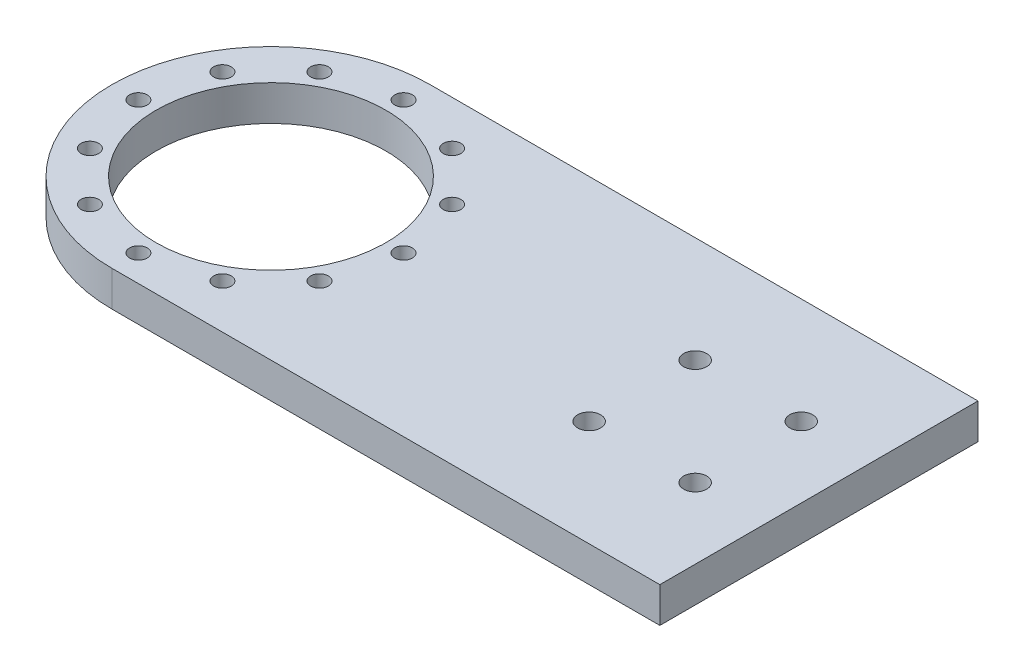
SolidWorks part; units mm, degrees
ref_plane "Front Plane" through (0, 0, 0) normal (0, 0, 1) x (1, 0, 0)
ref_plane "Top Plane" through (0, 0, 0) normal (0, 1, 0) x (1, 0, 0)
ref_plane "Right Plane" through (0, 0, 0) normal (1, 0, 0) x (0, 0, -1)
sketch "Sketch1" plane through (0, 0, 0) normal (0, 1, 0) x (1, 0, 0)
  line L0 (-55, 45) -> (100, 45)
  line L1 (-100, -45) -> (100, -45) construction
  line L2 (-100, -45) -> (-100, 45) construction
  line L3 (-100, 45) -> (100, 45) construction
  line L4 (100, -45) -> (100, 45) construction
  line L5 (0, 45) -> (0, -45) construction
  line L6 (-100, 0) -> (100, 0) construction
  line L7 (100, 45) -> (100, -45)
  line L8 (100, -45) -> (-55, -45)
  arc A1 (-55, 45) -> (-54.7588, -44.9994) centre (-55, 0) ccw
  point P0 (0, 0)
  dimension "D1" = 90
  dimension "D2" = 200
extrude "Boss-Extrude1" add sketch "Sketch1" along normal blind 10
sketch "Sketch2" plane through (0, 10, 0) normal (0, 1, 0) x (1, 0, 0)
  circle A0 centre (-55, 0) radius 37.5 construction
  circle A1 centre (-92.5, 0) radius 2.5
  circle A2 centre (-87.476, 18.75) radius 2.5
  circle A3 centre (-73.75, 32.476) radius 2.5
  circle A4 centre (-55, 0) radius 32.5
  circle A5 centre (-55, 37.5) radius 2.5
  circle A6 centre (-36.25, 32.476) radius 2.5
  circle A7 centre (-22.524, 18.75) radius 2.5
  circle A8 centre (-17.5, 0) radius 2.5
  circle A9 centre (-22.524, -18.75) radius 2.5
  circle A10 centre (-36.25, -32.476) radius 2.5
  circle A11 centre (-55, -37.5) radius 2.5
  circle A12 centre (-73.75, -32.476) radius 2.5
  circle A13 centre (-87.476, -18.75) radius 2.5
  point P11 (-55, 0)
  dimension "D1" = 75
  dimension "D2" = 5
  dimension "D4" = 65
  dimension "D3" = 12
extrude "Cut-Extrude1" cut sketch "Sketch2" against normal through all
sketch "Sketch3" plane through (0, 10, 0) normal (0, 1, 0) x (1, 0, 0)
  line L0 (100, 0) -> (-100, 0) construction
  line L1 (100, 45) -> (100, -45) construction
  line L3 (50, -15) -> (80, -15)
  line L4 (50, -15) -> (50, 15)
  line L5 (50, 15) -> (80, 15)
  line L6 (80, -15) -> (80, 15)
  line L7 (65, 15) -> (65, -15) construction
  line L8 (50, 0) -> (80, 0) construction
  arc A0 (-55, 45) -> (-55, -45) centre (-55, 0) ccw construction
  circle A1 centre (80, 15) radius 3.25
  circle A2 centre (50, 15) radius 3.25
  circle A3 centre (50, -15) radius 3.25
  circle A4 centre (80, -15) radius 3.25
  point P7 (65, 0)
  dimension "D1" = 6.5
  dimension "D2" = 30
  dimension "D3" = 30
  dimension "D4" = 20
extrude "Cut-Extrude2" cut sketch "Sketch3" against normal through all contours A2 | A1 | A4 | A3
